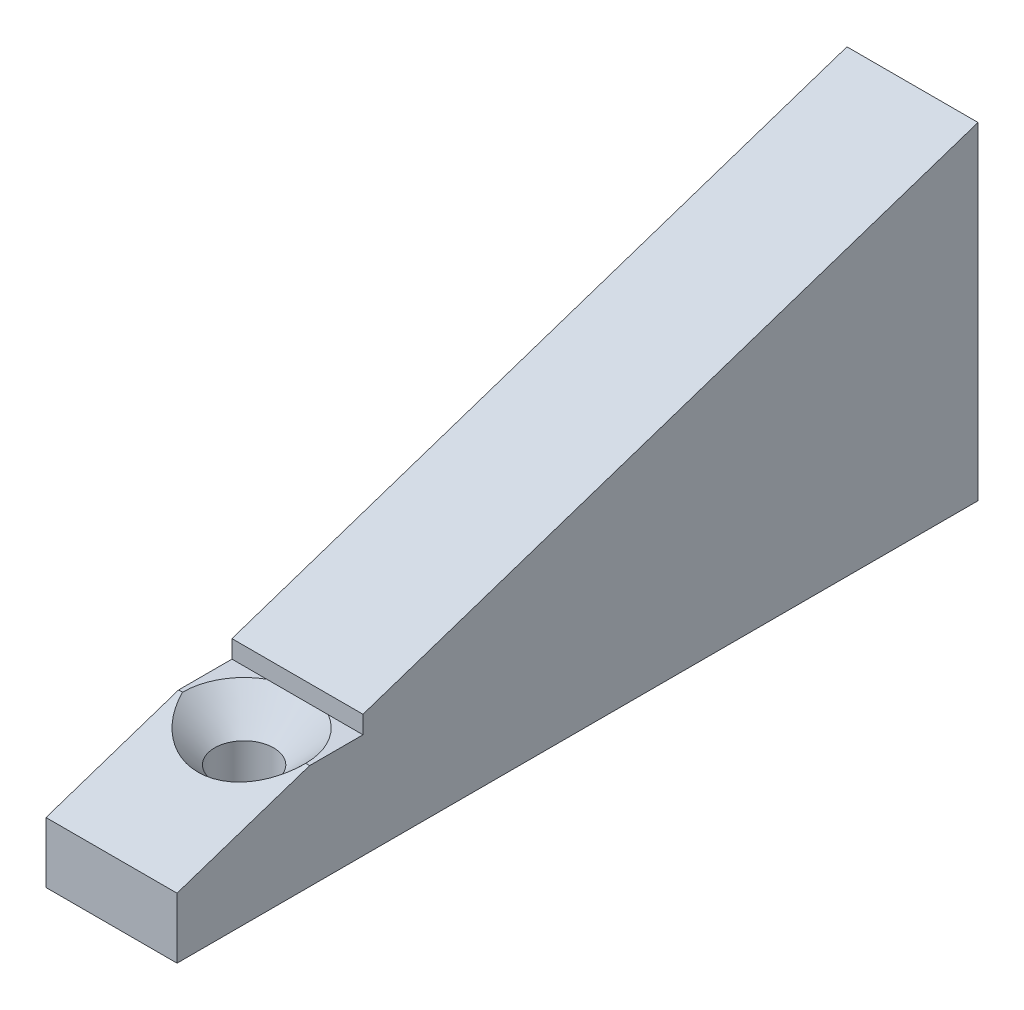
SolidWorks part; units mm, degrees
ref_plane "Front Plane" through (0, 0, 0) normal (0, 0, 1) x (1, 0, 0)
ref_plane "Top Plane" through (0, 0, 0) normal (0, 1, 0) x (1, 0, 0)
ref_plane "Right Plane" through (0, 0, 0) normal (1, 0, 0) x (0, 0, -1)
sketch "Sketch1" plane through (0, 0, 0) normal (1, 0, 0) x (0, 0, -1)
  line L0 (-18.7184, 4.6268) -> (-8.5988, 8)
  line L1 (42.4012, 25) -> (42.4012, 0)
  line L2 (42.4012, 0) -> (-18.7184, 0)
  line L3 (-4.5292, 9.3565) -> (-4.5292, 8)
  line L4 (-4.5292, 8) -> (-8.5988, 8)
  line L5 (-4.5292, 9.3565) -> (42.4012, 25)
  line L6 (-18.7184, 4.6268) -> (-18.7184, 0)
  dimension "D2" = 25
  dimension "D3" = 8
extrude "Boss-Extrude1" add sketch "Sketch1" along normal blind 10
hole_wizard "CSK for M4 Flat Head Machine Screw2" positions "Sketch8" profile "Sketch9" countersink size "M4" standard "ANSI Metric"
sketch "Sketch8" plane through (0, 8, 0) normal (0, 1, 0) x (1, 0, 0)
  line L0 (10, -8.5988) -> (0, -8.5988) construction
  point P5 (5, -8.5988)
  point P10 (0, 0)
  point P11 (0, 0)
sketch "Sketch9" plane through (5, 8, 8.5988) normal (1, 0, 0) x (0, 0, 1)
  line L0 (0, 0) -> (0, 11.3519)
  line L1 (0, 11.3519) -> (2.25, 10)
  line L2 (2.25, 10) -> (2.25, 2.45)
  line L3 (2.25, 2.45) -> (4.7, 0)
  line L5 (4.7, 0) -> (0, 0)
  line L6 (-2.25, 2.45) -> (-4.7, 0) construction
  line L10 (0, 11.3519) -> (-2.25, 10) construction
  line L11 (0, -6.35) -> (0, 107.95) construction
  dimension "Hole Dia." = 4.5
  dimension "Hole Depth" = 10
  dimension "Near C'Sink Dia." = 9.4
  dimension "Near C'Sink Angle" = 90
  dimension "Drill Angle" = 118
hole_wizard "Ø4.0mm Dowel Hole1" positions "3DSketch1" profile "Sketch10" hole size "Ø4.0" standard "ANSI Metric"
sketch3d "3DSketch1"
  line L0 (0, 0, -42.4012) -> (0, 25, -42.4012) construction
  line L1 (10, 25, -42.4012) -> (0, 25, -42.4012) construction
  line L2 (10, 0, -42.4012) -> (0, 0, -42.4012) construction
  point P0 (5, 18, -42.4012)
  point P2 (5, 7, -42.4012)
  dimension "D1" = 5
  dimension "D2" = 5
  dimension "D3" = 7
  dimension "D4" = 7
sketch "Sketch10" plane through (5, 18, -42.4012) normal (1, 0, 0) x (0, 1, 0)
  line L0 (0, 0) -> (0, 11.2017)
  line L1 (0, 11.2017) -> (2, 10)
  line L2 (2, 10) -> (2, 0)
  line L5 (2, 0) -> (0, 0)
  line L10 (0, 11.2017) -> (-2, 10) construction
  line L11 (0, -6.35) -> (0, 107.95) construction
  dimension "Hole Dia." = 4
  dimension "Hole Depth" = 10
  dimension "Drill Angle" = 118
